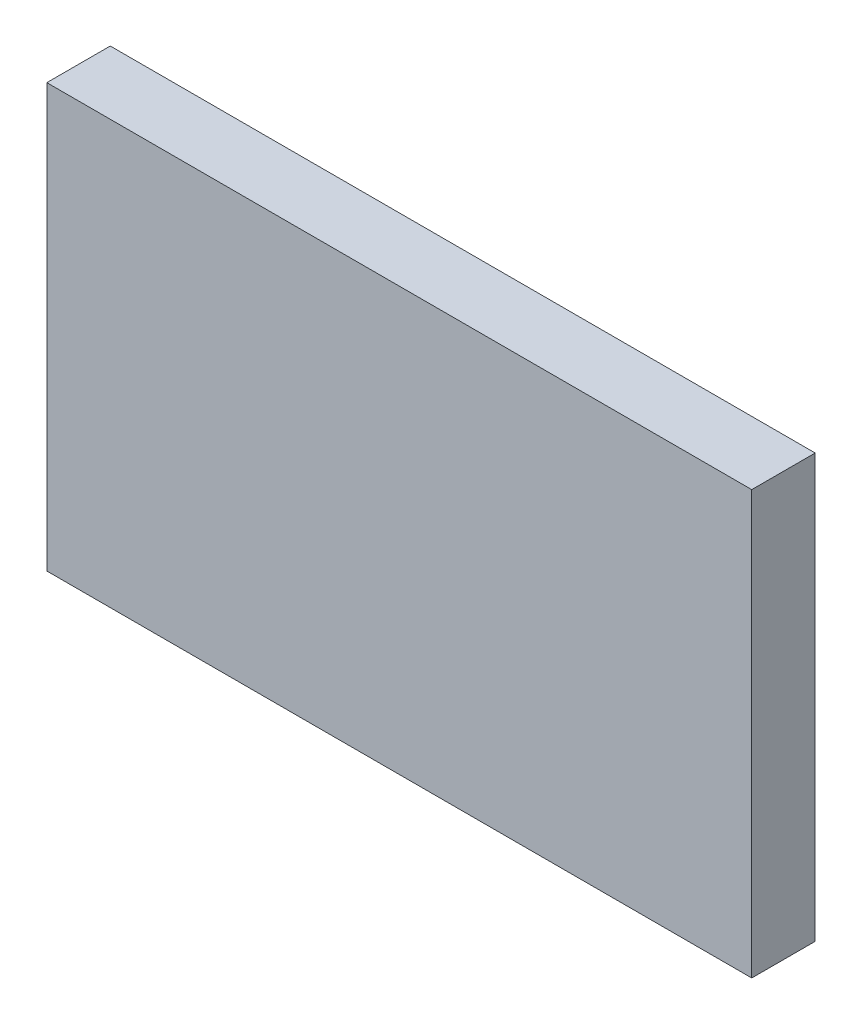
SolidWorks part; units mm, degrees
ref_plane "Front Plane" through (0, 0, 0) normal (0, 0, 1) x (1, 0, 0)
ref_plane "Top Plane" through (0, 0, 0) normal (0, 1, 0) x (1, 0, 0)
ref_plane "Right Plane" through (0, 0, 0) normal (1, 0, 0) x (0, 0, -1)
sketch "Sketch1" plane through (0, 0, 0) normal (0, 0, 1) x (1, 0, 0)
  line L1 (-33.8569, 31.4136) -> (66.1431, 31.4136)
  line L2 (-33.8569, 31.4136) -> (-33.8569, -28.5864)
  line L3 (-33.8569, -28.5864) -> (66.1431, -28.5864)
  line L4 (66.1431, 31.4136) -> (66.1431, -28.5864)
  dimension "D1" = 100
  dimension "D2" = 60
extrude "Boss-Extrude1" add sketch "Sketch1" along normal blind 9
